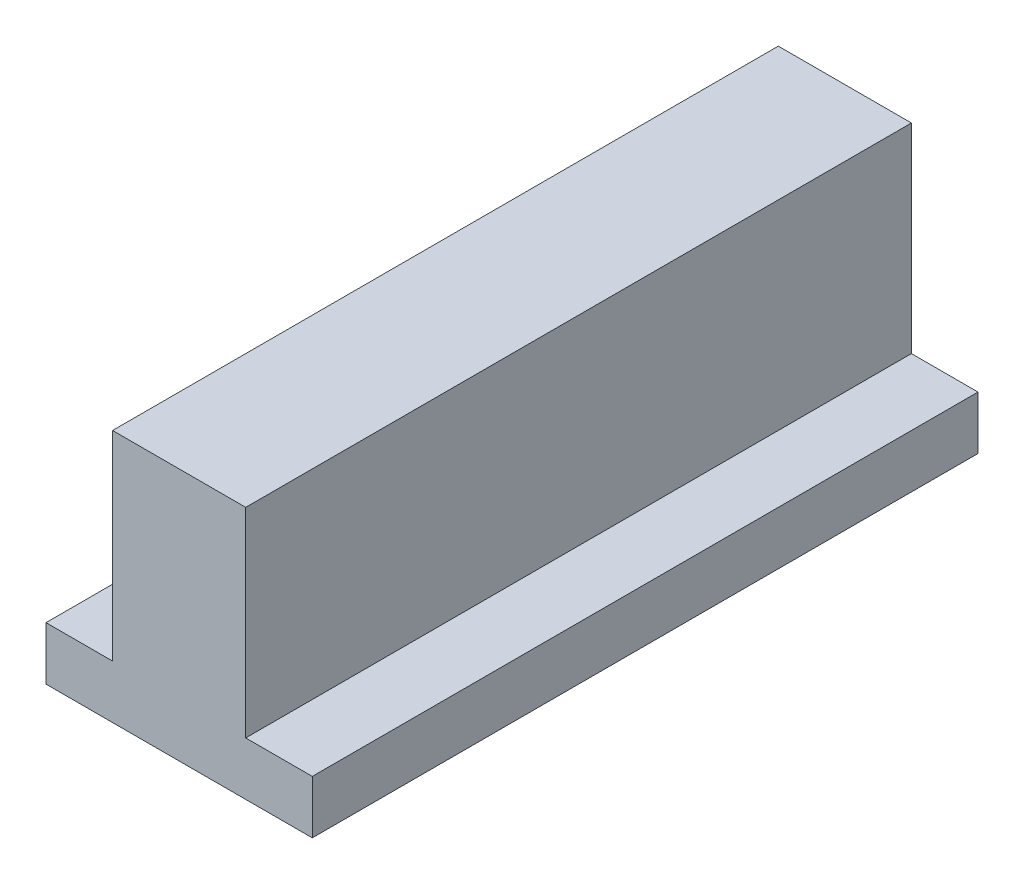
SolidWorks part; units mm, degrees
ref_plane "Front Plane" through (0, 0, 0) normal (0, 0, 1) x (1, 0, 0)
ref_plane "Top Plane" through (0, 0, 0) normal (0, 1, 0) x (1, 0, 0)
ref_plane "Right Plane" through (0, 0, 0) normal (1, 0, 0) x (0, 0, -1)
sketch "Sketch1" plane through (0, 0, 0) normal (0, 0, 1) x (1, 0, 0)
  line L0 (10, 0) -> (-10, 0)
  line L1 (0, 24.7212) -> (0, -43.2343) construction
  line L2 (-41.2644, 0) -> (34.5487, 0) construction
  line L3 (-10, 0) -> (-10, 4)
  line L4 (-10, 4) -> (-5, 4)
  line L5 (-5, 4) -> (-5, 9)
  line L6 (-5, 9) -> (22.1137, 9) construction
  line L7 (5, 19) -> (-5, 19)
  line L8 (10, 4) -> (5, 4)
  line L9 (10, 0) -> (10, 4)
  line L10 (5, 4) -> (5, 9)
  line L11 (5, 9) -> (5, 19)
  line L12 (-5, 9) -> (-5, 19)
  point P0 (-15, 4)
  point P8 (0, 0)
  point P12 (0, -20.5804)
  point P14 (0, -43.2343)
  point P15 (0, -43.2343)
  point P16 (0, -43.2343)
  point P29 (0, 19)
  dimension "D1" = 20
  dimension "D4" = 5
  dimension "D5" = 4
  dimension "D6" = 5
  dimension "D8" = 10
extrude "Boss-Extrude1" add sketch "Sketch1" along normal blind 50
